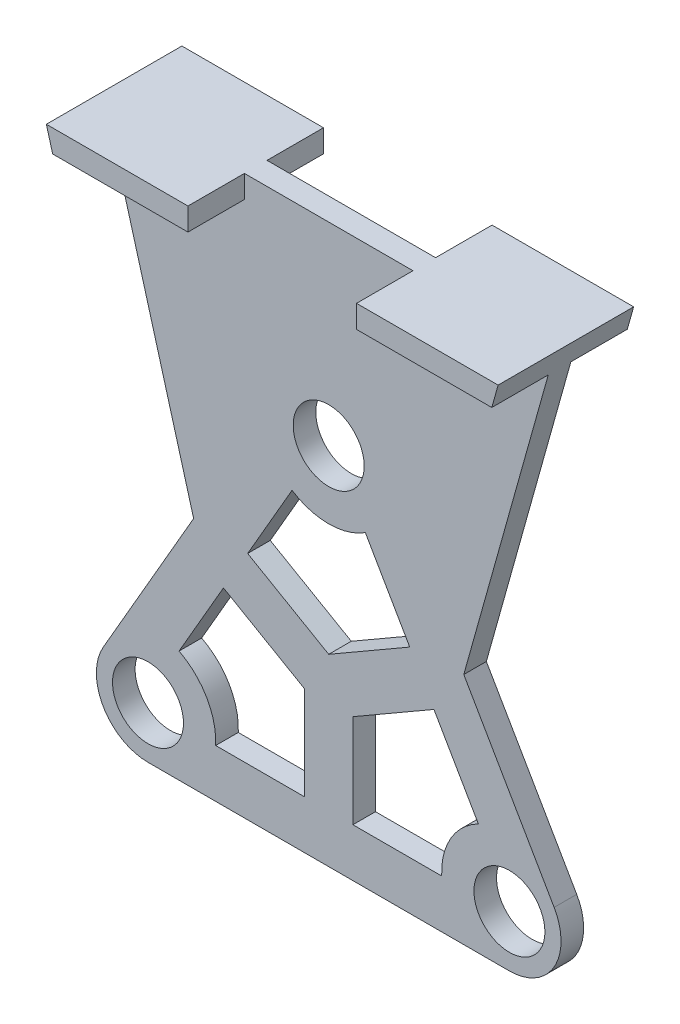
SolidWorks part; units mm, degrees
ref_plane "Front Plane" through (0, 0, 0) normal (0, 0, 1) x (1, 0, 0)
ref_plane "Top Plane" through (0, 0, 0) normal (0, 1, 0) x (1, 0, 0)
ref_plane "Right Plane" through (0, 0, 0) normal (1, 0, 0) x (0, 0, -1)
sketch "Sketch1" plane through (0, 0, 0) normal (0, 0, 1) x (1, 0, 0)
  line L0 (3.85, 0) -> (-3.85, 0) construction
  line L1 (42.1436, 104.9948) -> (-13.8564, 8)
  line L2 (69.8564, 104.9948) -> (125.8564, 8)
  line L3 (0, -16) -> (112, -16)
  circle A0 centre (0, 0) radius 11
  circle A1 centre (112, 0) radius 11
  arc A2 (-13.8564, 8) -> (0, -16) centre (0, 0) ccw
  arc A3 (112, -16) -> (125.8564, 8) centre (112, 0) ccw
  circle A4 centre (56, 96.9948) radius 11
  arc A5 (69.8564, 104.9948) -> (42.1436, 104.9948) centre (56, 96.9948) ccw
  dimension "D1" = 22
  dimension "D2" = 22
  dimension "D3" = 32
  dimension "D4" = 32
  dimension "D5" = 112
  dimension "D6" = 22
  dimension "D7" = 32
  dimension "D8" = 112
  dimension "D9" = 112
extrude "Boss-Extrude1" add sketch "Sketch1" along normal blind 7
sketch "Sketch2" plane through (0, 0, 7) normal (0, 0, 1) x (1, 0, 0)
  line L0 (9.6221, 18.6659) -> (23.384, 42.5022)
  line L1 (23.384, 42.5022) -> (48.5, 28.0015)
  line L2 (48.5, 28.0015) -> (48.5, -1)
  line L3 (48.5, -1) -> (20.9762, -1)
  line L4 (42.1436, 104.9948) -> (-13.8564, 8) construction
  line L5 (63.5, -1) -> (91.0238, -1)
  line L6 (63.5, -1) -> (63.5, 28.0015)
  line L7 (63.5, 28.0015) -> (88.616, 42.5022)
  line L8 (88.616, 42.5022) -> (102.3779, 18.6659)
  line L9 (125.8564, 8) -> (69.8564, 104.9948) construction
  line L10 (30.884, 55.4926) -> (44.6459, 79.3289)
  line L11 (30.884, 55.4926) -> (56, 40.9919)
  line L12 (56, 40.9919) -> (81.116, 55.4926)
  line L13 (81.116, 55.4926) -> (67.3541, 79.3289)
  line L14 (0, -16) -> (112, -16) construction
  line L15 (56, -16) -> (56, 32.3316) construction
  line L16 (97.8564, 56.4974) -> (56, 32.3316) construction
  line L17 (56, 32.3316) -> (14.1436, 56.4974) construction
  arc A0 (20.9762, -1) -> (9.6221, 18.6659) centre (0, 0) ccw
  circle A1 centre (0, 0) radius 11 construction
  arc A2 (44.6459, 79.3289) -> (67.3541, 79.3289) centre (56, 96.9948) ccw
  circle A3 centre (56, 96.9948) radius 11 construction
  arc A4 (102.3779, 18.6659) -> (91.0238, -1) centre (112, 0) ccw
  circle A5 centre (112, 0) radius 11 construction
  point P31 (35.942, 35.2519)
  dimension "D1" = 10
  dimension "D2" = 10
  dimension "D3" = 10
  dimension "D4" = 15
  dimension "D5" = 15
  dimension "D6" = 15
  dimension "D7" = 15
  dimension "D8" = 15
  dimension "D9" = 15
  dimension "D10" = 7.5
  dimension "D11" = 7.5
  dimension "D12" = 7.5
extrude "Cut-Extrude1" cut sketch "Sketch2" against normal through all
sketch "Sketch7" plane through (0, 0, 0) normal (0, 0, 1) x (1, 0, 0)
  line L0 (-14, 156.9948) -> (126, 156.9948)
  line L1 (14.1436, 56.4974) -> (-14, 156.9948)
  line L2 (42.1436, 104.9948) -> (-13.8564, 8) construction
  line L3 (126, 156.9948) -> (97.8564, 56.4974)
  line L4 (69.8564, 104.9948) -> (125.8564, 8) construction
  line L5 (97.8564, 56.4974) -> (69.8564, 104.9948)
  line L6 (14.1436, 56.4974) -> (42.1436, 104.9948)
  arc A0 (69.8564, 104.9948) -> (42.1436, 104.9948) centre (56, 96.9948) ccw
  point P2 (56, 156.9948)
  dimension "D1" = 60
  dimension "D2" = 140
extrude "Boss-Extrude2" add sketch "Sketch7" along normal blind 7
sketch "Sketch8" plane through (0, 0, 7) normal (0, 0, 1) x (1, 0, 0)
  line L0 (-12.0397, 149.9948) -> (124.0397, 149.9948)
  line L1 (-14, 156.9948) -> (14.1436, 56.4974) construction
  line L2 (97.8564, 56.4974) -> (126, 156.9948) construction
  line L3 (-12.0397, 149.9948) -> (-14, 156.9948)
  line L4 (-14, 156.9948) -> (126, 156.9948)
  line L5 (126, 156.9948) -> (124.0397, 149.9948)
  dimension "D1" = 7
extrude "Boss-Extrude3" add sketch "Sketch8" along normal blind 17.5
sketch "Sketch9" plane through (0, 0, 0) normal (0, 0, -1) x (-1, 0, 0)
  line L0 (-124.0397, 149.9948) -> (12.0397, 149.9948)
  line L1 (12.0397, 149.9948) -> (14, 156.9948)
  line L2 (14, 156.9948) -> (-126, 156.9948)
  line L3 (-126, 156.9948) -> (-124.0397, 149.9948)
extrude "Boss-Extrude4" add sketch "Sketch9" along normal blind 17.5
sketch "Sketch10" plane through (0, 156.9948, 0) normal (0, 1, 0) x (1, 0, 0)
  line L0 (29.88, -7) -> (29.88, -24.5)
  line L1 (-12.0397, -7) -> (124.0397, -7) construction
  line L2 (126, -24.5) -> (-14, -24.5) construction
  line L3 (29.88, -24.5) -> (82.12, -24.5)
  line L4 (82.12, -24.5) -> (82.12, -7)
  line L5 (82.12, -7) -> (29.88, -7)
  line L6 (29.88, 0) -> (29.88, 17.5)
  line L7 (-79.2, 0) -> (79.2, 0) construction
  line L8 (-14, 17.5) -> (126, 17.5) construction
  line L9 (29.88, 17.5) -> (82.12, 17.5)
  line L10 (82.12, 17.5) -> (82.12, 0)
  line L11 (82.12, 0) -> (29.88, 0)
  line L12 (126, -24.5) -> (126, 17.5) construction
  line L13 (-14, -24.5) -> (-14, 17.5) construction
  dimension "D1" = 43.88
  dimension "D2" = 43.88
extrude "Cut-Extrude2" cut sketch "Sketch10" against normal through all
